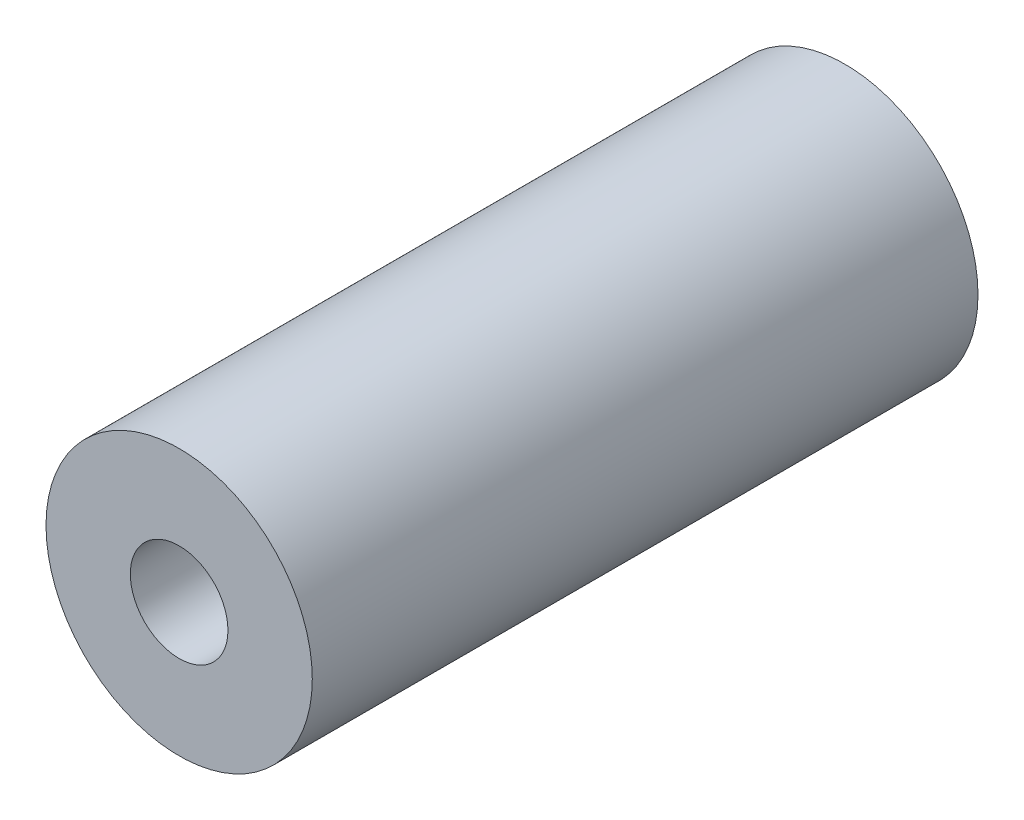
SolidWorks part; units mm, degrees
ref_plane "Plan de face" through (0, 0, 0) normal (0, 0, 1) x (1, 0, 0)
ref_plane "Plan de dessus" through (0, 0, 0) normal (0, 1, 0) x (1, 0, 0)
ref_plane "Plan de droite" through (0, 0, 0) normal (1, 0, 0) x (0, 0, -1)
sketch "Esquisse1" plane through (0, 0, 0) normal (0, 0, 1) x (1, 0, 0)
  circle A0 centre (0, 0) radius 2.2
  circle A1 centre (0, 0) radius 6
  dimension "D1" = 4.4
  dimension "D2" = 12
extrude "Boss.-Extru.1" add sketch "Esquisse1" along normal blind 30
